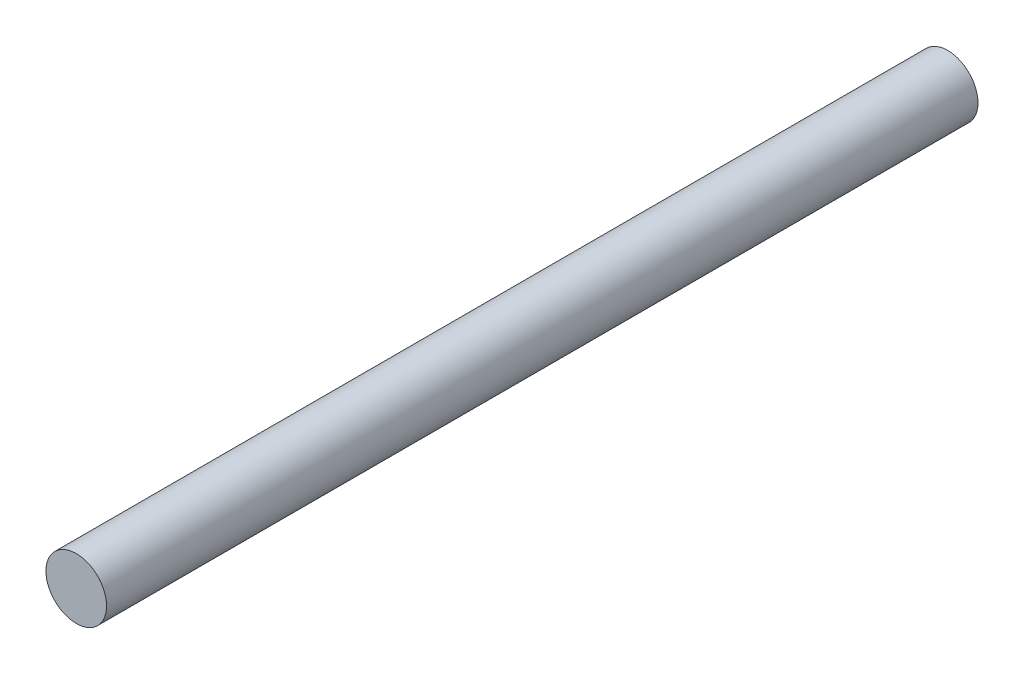
SolidWorks part; units mm, degrees
ref_plane "前视基准面" through (0, 0, 0) normal (0, 0, 1) x (1, 0, 0)
ref_plane "上视基准面" through (0, 0, 0) normal (0, 1, 0) x (1, 0, 0)
ref_plane "右视基准面" through (0, 0, 0) normal (1, 0, 0) x (0, 0, -1)
other "Configuration Table"
sketch "草图1" plane through (0, 0, 0) normal (0, 0, 1) x (1, 0, 0)
  line L0 (0, 0) -> (-6.2607, 0) construction
  line L1 (0, 0) -> (6.2607, 0) construction
  circle A0 centre (0, 0) radius 6.2607
  dimension "D1" = 12.5213
extrude "凸台-拉伸1" add sketch "草图1" along normal blind 180
